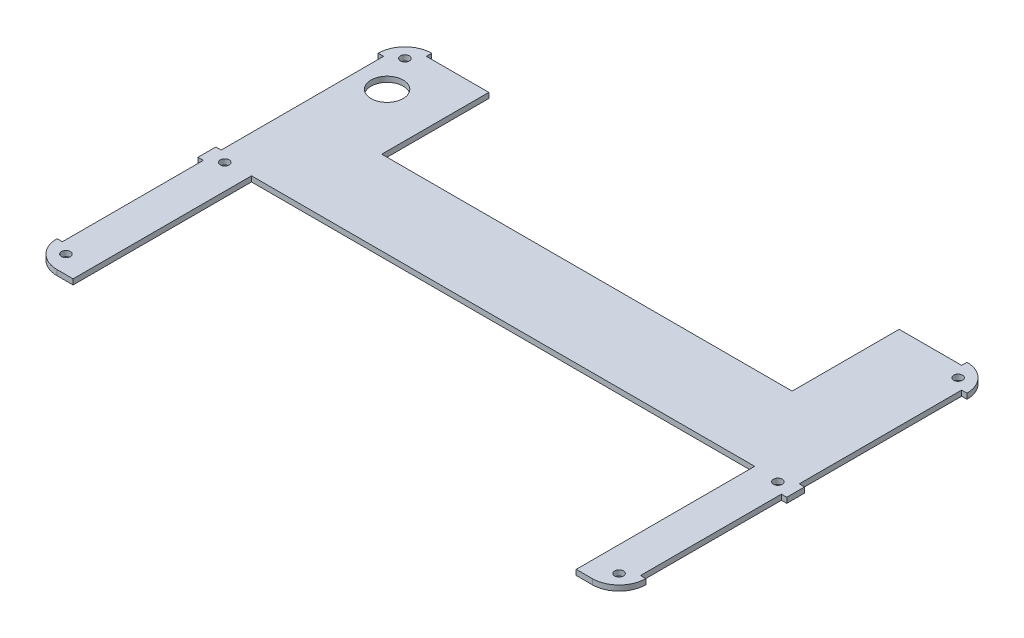
SolidWorks part; units mm, degrees
ref_plane "Plan de face" through (0, 0, 0) normal (0, 0, 1) x (1, 0, 0)
ref_plane "Plan de dessus" through (0, 0, 0) normal (0, 1, 0) x (1, 0, 0)
ref_plane "Plan de droite" through (0, 0, 0) normal (1, 0, 0) x (0, 0, -1)
sketch "Esquisse1" plane through (0, 0, 0) normal (0, 1, 0) x (1, 0, 0)
  line L0 (0, 200) -> (330, 200) construction
  line L1 (0, 0) -> (24, 0)
  line L2 (0, 0) -> (0, 210)
  line L3 (0, 210) -> (330, 210)
  line L4 (330, 0) -> (330, 210)
  line L6 (165, 210) -> (165, 0) construction
  line L7 (10, 210) -> (10, 0) construction
  line L8 (24, 0) -> (24, 100)
  line L9 (24, 100) -> (165, 100)
  line L10 (0, 0) -> (330, 0) construction
  line L11 (306, 0) -> (306, 100)
  line L12 (330, 0) -> (306, 0)
  line L24 (306, 100) -> (165, 100)
  circle A0 centre (10, 200) radius 2.5
  circle A1 centre (320, 200) radius 2.5
  circle A2 centre (10, 99) radius 2.5
  circle A3 centre (320, 99) radius 2.5
  circle A4 centre (10, 10) radius 2.5
  circle A5 centre (320, 10) radius 2.5
  circle A6 centre (20, 180) radius 9
  point P13 (10, 200)
  dimension "D3" = 5
  dimension "D12" = 5
  dimension "D8" = 18
  dimension "D9" = 20
  dimension "D10" = 30
  dimension "D1" = 330
  dimension "D2" = 210
  dimension "D4" = 10
  dimension "D5" = 10
  dimension "D6" = 14
  dimension "D7" = 100
  dimension "D13" = 101
  dimension "D16" = 89
extrude "Extrusion1" add sketch "Esquisse1" along normal blind 3
fillet "Congé1" radius 15 4 edges at (0, 1.5, 0) (330, 1.5, 0) (330, 1.5, -210) (0, 1.5, -210)
sketch "Esquisse2" plane through (0, 3, 0) normal (0, 1, 0) x (1, 0, 0)
  line L0 (165, 210) -> (165, 100) construction
  line L1 (315, 210) -> (15, 210) construction
  line L2 (24, 100) -> (306, 100) construction
  line L3 (15, 210) -> (15, 207)
  line L4 (15, 207) -> (315, 207)
  line L5 (15, 210) -> (315, 210)
  line L6 (0, 195) -> (3, 195)
  line L7 (3, 195) -> (3, 104)
  line L8 (3, 104) -> (0, 104)
  line L9 (0, 195) -> (0, 15) construction
  line L10 (0, 104) -> (0, 195)
  line L11 (0, 15) -> (3, 15)
  line L12 (3, 15) -> (3, 94)
  line L13 (3, 94) -> (0, 94)
  line L14 (10, 99) -> (0, 99) construction
  line L15 (320, 99) -> (330, 99) construction
  line L16 (327, 94) -> (330, 94)
  line L17 (327, 15) -> (327, 94)
  line L18 (330, 15) -> (327, 15)
  line L19 (330, 104) -> (330, 195)
  line L20 (327, 104) -> (330, 104)
  line L21 (327, 195) -> (327, 104)
  line L22 (330, 195) -> (327, 195)
  line L23 (315, 210) -> (315, 207)
  line L24 (0, 94) -> (0, 15)
  line L25 (330, 94) -> (330, 15)
  point P39 (165, 207)
  dimension "D1" = 3
  dimension "D2" = 3
  dimension "D3" = 5
  dimension "D4" = 5
extrude "Extrusion2" cut sketch "Esquisse2" against normal up to next
sketch "Esquisse3" plane through (0, 3, 0) normal (0, 1, 0) x (1, 0, 0)
  line L0 (165, 207) -> (165, 100) construction
  line L1 (15, 207) -> (315, 207) construction
  line L2 (24, 100) -> (306, 100) construction
  line L3 (3, 147) -> (327, 147) construction
  line L4 (3, 104) -> (3, 195) construction
  line L5 (327, 195) -> (327, 104) construction
  line L6 (50, 207) -> (50, 147)
  line L7 (50, 147) -> (280, 147)
  line L8 (50, 207) -> (280, 207)
  line L9 (280, 207) -> (280, 147)
  point P17 (165, 147)
  dimension "D1" = 60
  dimension "D2" = 115
extrude "Extrusion3" cut sketch "Esquisse3" against normal up to next
